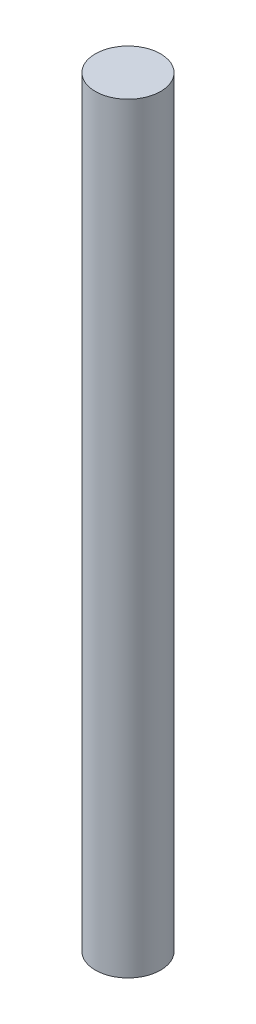
SolidWorks part; units mm, degrees
ref_plane "Front Plane" through (0, 0, 0) normal (0, 0, 1) x (1, 0, 0)
ref_plane "Top Plane" through (0, 0, 0) normal (0, 1, 0) x (1, 0, 0)
ref_plane "Right Plane" through (0, 0, 0) normal (1, 0, 0) x (0, 0, -1)
sketch "Sketch1" plane through (0, 0, 0) normal (0, 1, 0) x (1, 0, 0)
  circle A0 centre (0, 0) radius 3
  dimension "D1" = 6
extrude "Boss-Extrude1" add sketch "Sketch1" along normal blind 70
